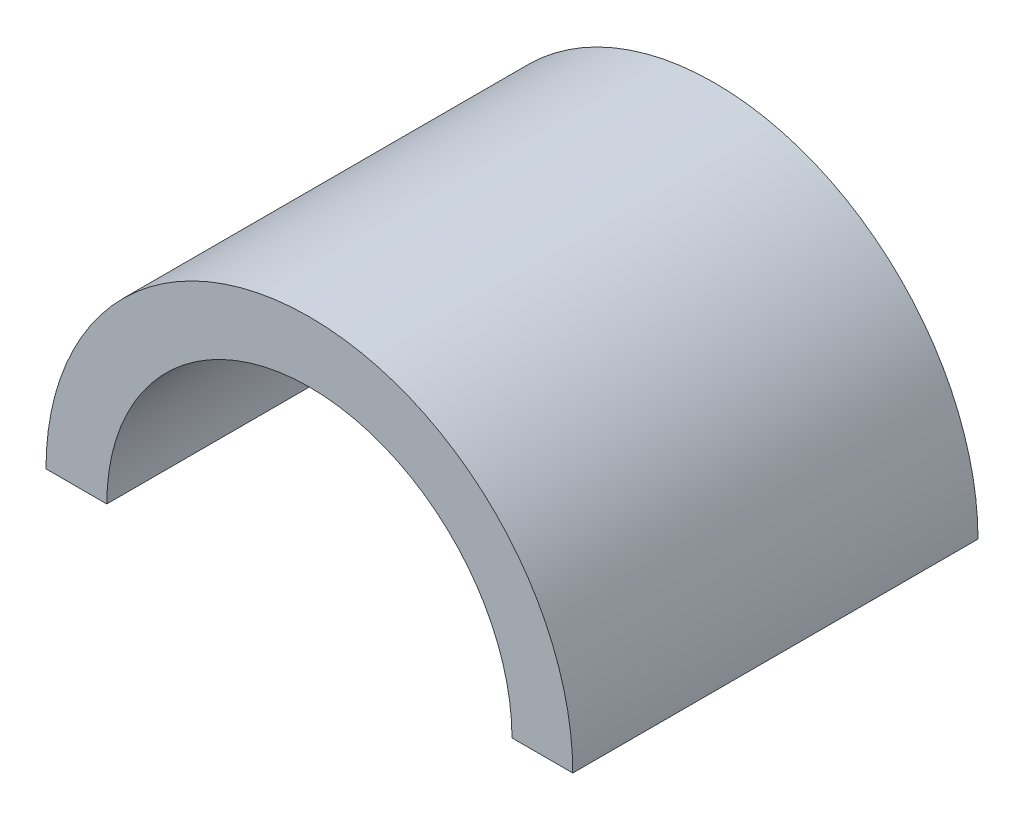
SolidWorks part; units mm, degrees
ref_plane "Front Plane" through (0, 0, 0) normal (0, 0, 1) x (1, 0, 0)
ref_plane "Top Plane" through (0, 0, 0) normal (0, 1, 0) x (1, 0, 0)
ref_plane "Right Plane" through (0, 0, 0) normal (1, 0, 0) x (0, 0, -1)
sketch "Sketch1" plane through (0, 0, 0) normal (0, 0, 1) x (1, 0, 0)
  line L0 (120.65, 0) -> (177.8, 0)
  line L1 (0, 0) -> (57.15, 0)
  line L2 (0, 0) -> (0, 12.7)
  line L3 (0, 12.7) -> (49.6274, 12.7)
  line L4 (177.8, 0) -> (177.8, 12.7)
  line L5 (128.1726, 12.7) -> (177.8, 12.7)
  arc A0 (120.65, 0) -> (57.15, 0) centre (88.9, 0) ccw
  arc A1 (130.175, 0) -> (47.625, 0) centre (88.9, 0) ccw
  point P11 (0, 0)
  point P13 (0, 0)
  point P14 (0, 0)
  point P15 (0, 0)
  point P16 (0, 0)
  dimension "D3" = 31.75
  dimension "D4" = 41.275
  dimension "D1" = 12.7
  dimension "D2" = 177.8
  dimension "D5" = 88.9
  dimension "D6" = 49.6274
extrude "Boss-Extrude1" add sketch "Sketch1" along normal mid plane 63.5 contours L0 A1 L1 A0
